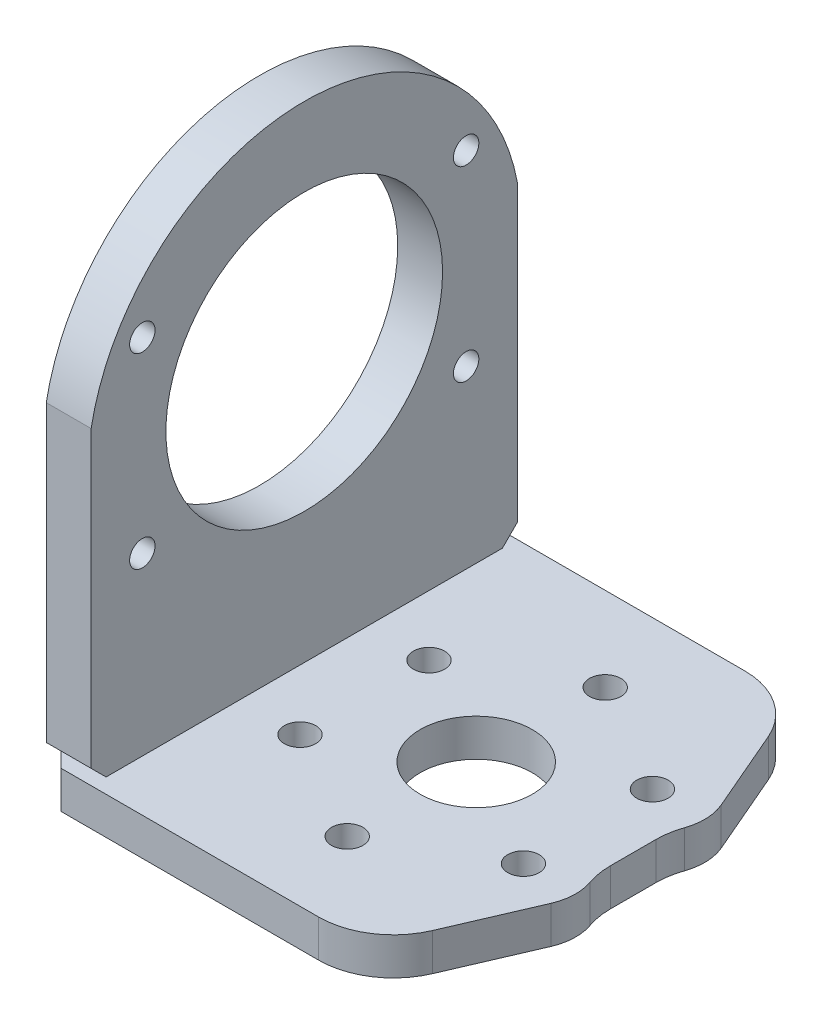
SolidWorks part; units mm, degrees
material "5052-H32"
ref_plane "前视基准面" through (0, 0, 0) normal (0, 0, 1) x (1, 0, 0)
ref_plane "上视基准面" through (0, 0, 0) normal (0, 1, 0) x (1, 0, 0)
ref_plane "右视基准面" through (0, 0, 0) normal (1, 0, 0) x (0, 0, -1)
other "Configuration Table"
sketch "草图1" plane through (0, 0, 0) normal (0, 1, 0) x (1, 0, 0)
  line L1 (-29, 28.5) -> (29, 28.5)
  line L2 (-29, 28.5) -> (-29, -28.5)
  line L3 (-29, -28.5) -> (29, -28.5)
  line L4 (29, 28.5) -> (29, -28.5)
  line L5 (-29, 28.5) -> (29, -28.5) construction
  line L6 (-29, -28.5) -> (29, 28.5) construction
  point P0 (0, 0)
  dimension "D1" = 57
  dimension "D2" = 58
extrude "凸台-拉伸1" add sketch "草图1" along normal blind 5
sketch "草图5" plane through (0, 5, 0) normal (0, 1, 0) x (1, 0, 0)
  line L0 (-29, 28.5) -> (-29, -28.5) construction
  line L1 (-26, 21) -> (26, 21) construction
  line L2 (-26, 21) -> (-26, -21) construction
  line L3 (-26, -21) -> (26, -21) construction
  line L4 (26, 21) -> (26, -21) construction
  line L5 (-26, 21) -> (26, -21) construction
  line L6 (-26, -21) -> (26, 21) construction
  circle A0 centre (-26, 21) radius 1
  circle A1 centre (-26, -21) radius 1
  circle A2 centre (26, -21) radius 1 construction
  circle A3 centre (26, 21) radius 1 construction
  circle A4 centre (0, 17.25) radius 2.1
  circle A5 centre (0, 0) radius 17.25 construction
  circle A6 centre (14.9389, 8.625) radius 2.1
  circle A7 centre (14.9389, -8.625) radius 2.1
  circle A8 centre (0, -17.25) radius 2.1
  circle A9 centre (-14.9389, -8.625) radius 2.1
  circle A10 centre (-14.9389, 8.625) radius 2.1
  point P0 (0, 0)
  point P28 (0, 0)
  dimension "D3" = 2
  dimension "D4" = 34.5
  dimension "D6" = 4.2
  dimension "D1" = 3
  dimension "D2" = 42
  dimension "D5" = 6
extrude "切除-拉伸2" cut sketch "草图5" against normal through all
hole_wizard "M3 十字槽沉头木螺钉的锥形沉头孔1" positions "3D草图2" profile "草图8" countersink size "M3" standard "GB"
sketch3d "3D草图2"
  line L0 (-26, 0, 21) -> (-26, 5, 21) construction
  line L1 (-26, 0, -21) -> (-26, 5, -21) construction
  point P0 (-26, 0, 21)
  point P4 (-26, 0, -21)
sketch "草图8" plane through (-26, 0, 21) normal (1, 0, 0) x (0, 0, -1)
  line L0 (0, 0) -> (0, 6.5215)
  line L1 (0, 6.5215) -> (1.7, 5.5)
  line L2 (1.7, 5.5) -> (1.7, 1.6)
  line L3 (1.7, 1.6) -> (3.3, 0)
  line L5 (3.3, 0) -> (0, 0)
  line L6 (-1.7, 1.6) -> (-3.3, 0) construction
  line L10 (0, 6.5215) -> (-1.7, 5.5) construction
  line L11 (0, -6.35) -> (0, 107.95) construction
  dimension "孔直径" = 3.4
  dimension "孔深度" = 5.5
  dimension "近端锥形沉头孔直径" = 6.6
  dimension "近端锥形沉头孔角度" = 90
  dimension "导头角度" = 118
chamfer "倒角1" distance 2 angle 45 4 edges at (29, 2.5, -28.5) (29, 2.5, 28.5) (-29, 2.5, -28.5) (-29, 2.5, 28.5)
sketch "草图9" plane through (0, 5, 0) normal (0, 1, 0) x (1, 0, 0)
  line L1 (-29, 28.5) -> (-23, 28.5)
  line L2 (-29, 28.5) -> (-29, -28.5)
  line L3 (-29, -28.5) -> (-23, -28.5)
  line L4 (-23, 28.5) -> (-23, -28.5)
  line L5 (-29, 26.5) -> (-29, -26.5) construction
  line L6 (27, 28.5) -> (-27, 28.5) construction
  line L7 (-27, -28.5) -> (27, -28.5) construction
  dimension "D1" = 6
extrude "凸台-拉伸3" add sketch "草图9" along normal blind 68 separate body
sketch "草图10" plane through (-23, 0, 0) normal (1, 0, 0) x (0, 0, -1)
  line L0 (26.5, 5) -> (-26.5, 5) construction
  circle A0 centre (0, 41) radius 18.5
  dimension "D1" = 37
  dimension "D2" = 36
extrude "切除-拉伸3" cut sketch "草图10" against normal through all
chamfer "倒角2" distance 2 angle 45 2 edges at (-26, 5, 28.5) (-26, 5, -28.5)
sketch "草图11" plane through (0, 5, 0) normal (0, 1, 0) x (1, 0, 0)
  circle A0 centre (0, 0) radius 7.5
  dimension "D1" = 15
extrude "切除-拉伸4" cut sketch "草图11" against normal through all
sketch "草图12" plane through (-29, 0, 0) normal (-1, 0, 0) x (0, 0, 1)
  circle A0 centre (0, 41) radius 25 construction
  circle A1 centre (0, 66) radius 1 construction
  circle A2 centre (21.6506, 53.5) radius 1
  circle A3 centre (21.6506, 28.5) radius 1
  circle A4 centre (0, 16) radius 1 construction
  circle A5 centre (-21.6506, 28.5) radius 1
  circle A6 centre (-21.6506, 53.5) radius 1
  point P17 (0, 41)
  dimension "D1" = 50
  dimension "D2" = 2
  dimension "D3" = 6
extrude "切除-拉伸5" cut sketch "草图12" against normal through all
hole_wizard "M3 六角圆柱头螺钉的柱形沉头孔1" positions "3D草图3" profile "草图13" counterbore size "M3" standard "GB" end condition up to next
sketch3d "3D草图3"
  circle A0 centre (-29, 28.5, -21.6506) radius 1 construction
  circle A1 centre (-29, 28.5, 21.6506) radius 1 construction
  circle A2 centre (-29, 53.5, 21.6506) radius 1 construction
  circle A3 centre (-29, 53.5, -21.6506) radius 1 construction
  point P0 (-29, 53.5, -21.6506)
  point P2 (-29, 53.5, 21.6506)
  point P4 (-29, 28.5, 21.6506)
  point P6 (-29, 28.5, -21.6506)
  point P11 (-30, 28.5, -21.6506)
  point P15 (-30, 28.5, 21.6506)
  point P19 (-30, 53.5, 21.6506)
  point P23 (-30, 53.5, -21.6506)
sketch "草图13" plane through (-29, 53.5, -21.6506) normal (0, 1, 0) x (0, 0, 1)
  line L0 (0, 0) -> (0, 58)
  line L1 (0, 58) -> (1.7, 58)
  line L3 (1.7, 58) -> (1.7, 3.4)
  line L4 (1.7, 3.4) -> (3, 3.4)
  line L5 (3, 3.4) -> (3, 0)
  line L7 (3, 0) -> (0, 0)
  line L11 (0, -6.35) -> (0, 107.95) construction
  dimension "通孔孔直径" = 3.4
  dimension "通孔孔深度" = 58
  dimension "柱形沉头孔直径" = 6
  dimension "柱形沉头孔深度" = 3.4
sketch "草图14" plane through (-29, 0, 0) normal (-1, 0, 0) x (0, 0, 1)
  line L7 (-28.5, 73) -> (-28.5, 7) construction
  line L8 (28.5, 73) -> (28.5, 7) construction
  line L9 (-28.5, 73) -> (28.5, 73) construction
  line L10 (28.5, 73) -> (28.5, 46.3619)
  line L11 (-28.5, 73) -> (28.5, 73)
  line L12 (-28.5, 73) -> (-28.5, 46.3619)
  arc A2 (28.5, 46.3619) -> (-28.5, 46.3619) centre (0, 41) ccw
  circle A4 centre (0, 41) radius 18.5 construction
  point P1 (-28.5, 57.0733)
  point P2 (-28.5, 48.9481)
  point P9 (0, 43.1294)
  point P12 (-28.5, 46.9713)
  point P13 (-28.5, 48.0438)
  line M10 (28.5, 7) -> (28.5, 73)
  line M11 (28.5, 73) -> (-28.5, 73)
  line M12 (-28.5, 73) -> (-28.5, 7)
  dimension "D1" = 58
extrude "切除-拉伸6" cut sketch "草图14" against normal blind 10 contours A2 M10 M11 M12
sketch "草图15" plane through (0, 0, -28.5) normal (0, 0, -1) x (-1, 0, 0)
  line L0 (-27, 5) -> (27, 5) construction
  line L1 (-27, 5) -> (-27, 0) construction
  circle A0 centre (0, 2.5) radius 0.05
  point P4 (0, 5)
  point P7 (-27, 2.5)
  dimension "D1" = 0.1
extrude "切除-拉伸7" cut sketch "草图15" against normal blind 0.1
sketch "草图16" plane through (-29, 0, 0) normal (-1, 0, 0) x (0, 0, 1)
  line L0 (-26.5, 5) -> (-26.5, 0) construction
  circle A0 centre (0, 2.5) radius 0.05
  point P5 (-26.5, 2.5)
  dimension "D1" = 0.1
extrude "切除-拉伸8" cut sketch "草图16" against normal blind 0.1
sketch "草图17" plane through (0, 5, 0) normal (0, 1, 0) x (1, 0, 0)
  line L0 (14, 28.5) -> (21.3679, 11.3941)
  line L1 (27, 28.5) -> (-27, 28.5) construction
  line L2 (-29, 26.5) -> (-29, -26.5) construction
  line L3 (-31.9, 0) -> (31.9, 0) construction
  line L4 (14, -28.5) -> (21.3679, -11.3941)
  line L5 (21, 5.1231) -> (21, -5.1231)
  line L6 (-27, -28.5) -> (27, -28.5) construction
  line L7 (27, -28.5) -> (29, -26.5) construction
  line L8 (29, -26.5) -> (29, 26.5) construction
  line L9 (29, 26.5) -> (27, 28.5) construction
  line L10 (14, -28.5) -> (27, -28.5)
  line L11 (27, -28.5) -> (29, -26.5)
  line L12 (29, -26.5) -> (29, 26.5)
  line L13 (29, 26.5) -> (27, 28.5)
  line L14 (27, 28.5) -> (14, 28.5)
  arc A0 (21, 5.1231) -> (21.3679, 11.3941) centre (14.9389, 8.625) ccw
  arc A1 (21, -5.1231) -> (21.3679, -11.3941) centre (14.9389, -8.625) cw
  circle A2 centre (14.9389, 8.625) radius 2.1 construction
  dimension "D1" = 14
  dimension "D2" = 43
  dimension "D3" = 50
extrude "切除-拉伸9" cut sketch "草图17" against normal blind 10
fillet "圆角1" radius 10 4 edges at (14, 2.5, -28.5) (14, 2.5, 28.5) (21, 2.5, 5.1231) (21, 2.5, -5.1231)
sketch "草图18" plane through (0, 0, 0) normal (0, -1, 0) x (1, 0, 0)
  circle A0 centre (-26, 0) radius 1.65
  point P2 (-26, 21)
  dimension "D1" = 3.3
extrude "切除-拉伸10" cut sketch "草图18" against normal up to surface (5 mm away) up to face at (4.7407, 5, 0)
hole_wizard "M3 螺纹孔1" positions "3D草图4" profile "草图21" tap size "M3" standard "GB"
sketch3d "3D草图4"
  circle A0 centre (-26, 1.6, -21) radius 1.7 construction
  circle A1 centre (-26, 0, 0) radius 1.65 construction
  circle A2 centre (-26, 1.6, 21) radius 1.7 construction
  point P0 (-26, 5, -21)
  point P2 (-26, 5, 0)
  point P4 (-26, 5, 21)
  point P9 (-26, -0.1, -21)
  point P13 (-26, -1.65, 0)
  point P17 (-26, -0.1, 21)
sketch "草图21" plane through (-26, 5, -21) normal (1, 0, 0) x (0, 0, -1)
  line L0 (0, 0) -> (0, 6.7511)
  line L1 (0, 6.7511) -> (1.25, 6)
  line L2 (1.25, 6) -> (1.25, 0)
  line L5 (1.25, 0) -> (0, 0)
  line L10 (0, 6.7511) -> (-1.25, 6) construction
  line L11 (0, -6.35) -> (0, 107.95) construction
  dimension "螺纹孔钻头直径" = 2.5
  dimension "螺纹孔钻头深度" = 6
  dimension "导头角度" = 118
cosmetic thread "孔螺蚊线1" parameters "D1"=6, "D2"=3
cosmetic thread "孔螺蚊线2" parameters "D1"=6, "D2"=3
cosmetic thread "孔螺蚊线3" parameters "D1"=6, "D2"=3
